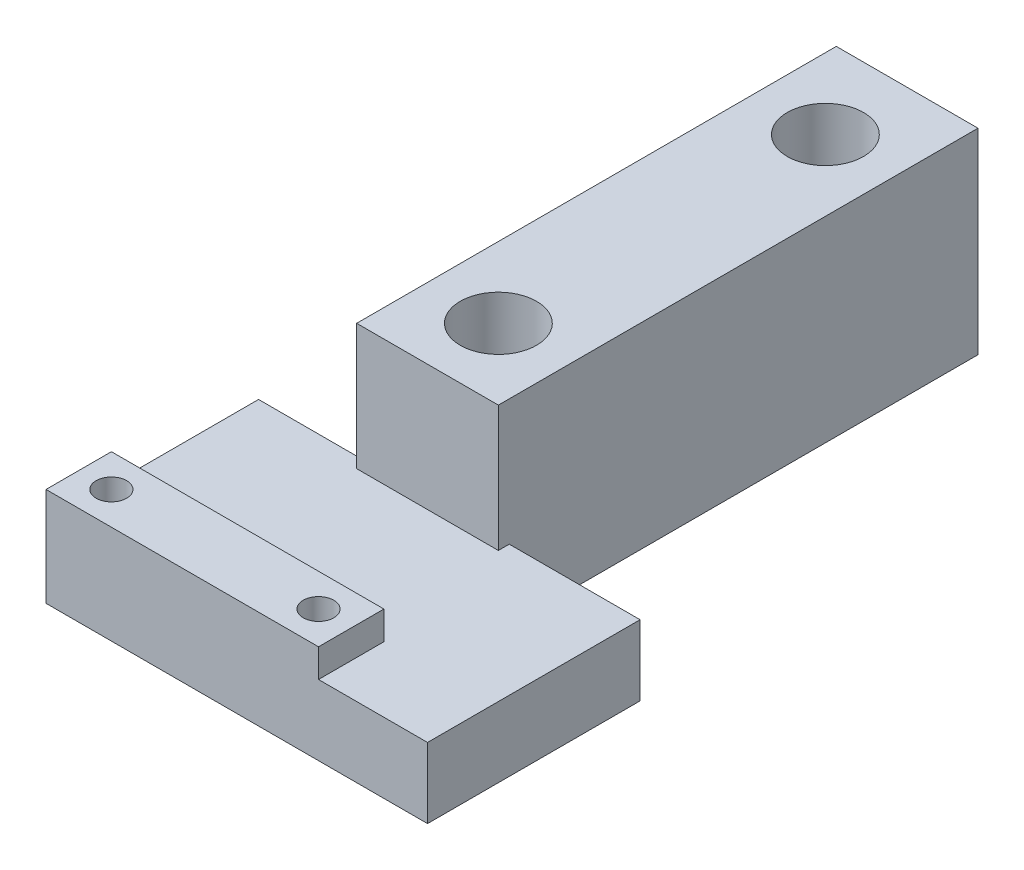
SolidWorks part; units mm, degrees
ref_plane "Front" through (0, 0, 0) normal (0, 0, 1) x (1, 0, 0)
ref_plane "Top" through (0, 0, 0) normal (0, 1, 0) x (1, 0, 0)
ref_plane "Right" through (0, 0, 0) normal (1, 0, 0) x (0, 0, -1)
sketch "Sketch1" plane through (0, 0, 0) normal (0, 1, 0) x (1, 0, 0)
  line L1 (-17.5, -9.75) -> (17.5, -9.75)
  line L2 (-17.5, -9.75) -> (-17.5, 9.75)
  line L3 (-17.5, 9.75) -> (17.5, 9.75)
  line L4 (17.5, -9.75) -> (17.5, 9.75)
  line L5 (-17.5, -9.75) -> (17.5, 9.75) construction
  line L6 (-17.5, 9.75) -> (17.5, -9.75) construction
  point P0 (0, 0)
  dimension "D1" = 35
  dimension "D2" = 19.5
extrude "Boss-Extrude1" add sketch "Sketch1" along normal blind 6.45
sketch "Sketch2" plane through (0, 0, 0) normal (0, 1, 0) x (1, 0, 0)
  line L0 (17.5, 9.75) -> (-17.5, 9.75) construction
  line L1 (-7.5, 52.75) -> (5.5, 52.75)
  line L2 (-7.5, 52.75) -> (-7.5, 8.75)
  line L3 (-7.5, 8.75) -> (5.5, 8.75)
  line L4 (5.5, 52.75) -> (5.5, 8.75)
  line L5 (-7.5, 52.75) -> (5.5, 8.75) construction
  line L6 (-7.5, 8.75) -> (5.5, 52.75) construction
  line L7 (-17.5, 9.75) -> (-17.5, -9.75) construction
  point P0 (-1, 30.75)
  dimension "D1" = 13
  dimension "D2" = 44
  dimension "D3" = 1
  dimension "D4" = 10
extrude "Boss-Extrude2" add sketch "Sketch2" along normal blind 18
sketch "Sketch3" plane through (0, 18, 0) normal (0, 1, 0) x (1, 0, 0)
  line L0 (5.5, 52.75) -> (-7.5, 52.75) construction
  line L1 (-7.5, 52.75) -> (-7.5, 8.75) construction
  line L2 (-7.5, 8.75) -> (5.5, 8.75) construction
  circle A0 centre (-1, 45.25) radius 3.5
  circle A1 centre (-1, 15.25) radius 3.5
  point P10 (0, 0)
  dimension "D1" = 7
  dimension "D2" = 7.5
  dimension "D3" = 6.5
  dimension "D4" = 6.5
extrude "Cut-Extrude1" cut sketch "Sketch3" against normal through all
sketch "Sketch4" plane through (0, 6.45, 0) normal (0, 1, 0) x (1, 0, 0)
  line L0 (-17.5, 9.75) -> (-17.5, -9.75) construction
  line L1 (-17.5, -3.75) -> (7.5, -3.75)
  line L2 (-17.5, -3.75) -> (-17.5, -9.75)
  line L3 (-17.5, -9.75) -> (7.5, -9.75)
  line L4 (7.5, -3.75) -> (7.5, -9.75)
  line L5 (-17.5, -3.75) -> (7.5, -9.75) construction
  line L6 (-17.5, -9.75) -> (7.5, -3.75) construction
  line L7 (-17.5, -9.75) -> (17.5, -9.75) construction
  point P0 (-5, -6.75)
  dimension "D1" = 6
  dimension "D2" = 25
extrude "Boss-Extrude3" add sketch "Sketch4" along normal blind 2.6
sketch "Sketch5" plane through (0, 9.05, 0) normal (0, 1, 0) x (1, 0, 0)
  line L0 (-17.5, -3.75) -> (-17.5, -9.75) construction
  line L1 (7.5, -3.75) -> (-17.5, -3.75) construction
  line L2 (7.5, -9.75) -> (7.5, -3.75) construction
  circle A0 centre (-14.5, -6.75) radius 1.4
  circle A1 centre (4.5, -6.75) radius 1.4
  point P8 (0, 0)
  dimension "D1" = 2.8
  dimension "D2" = 3
  dimension "D3" = 3
  dimension "D4" = 3
extrude "Cut-Extrude2" cut sketch "Sketch5" against normal through all
